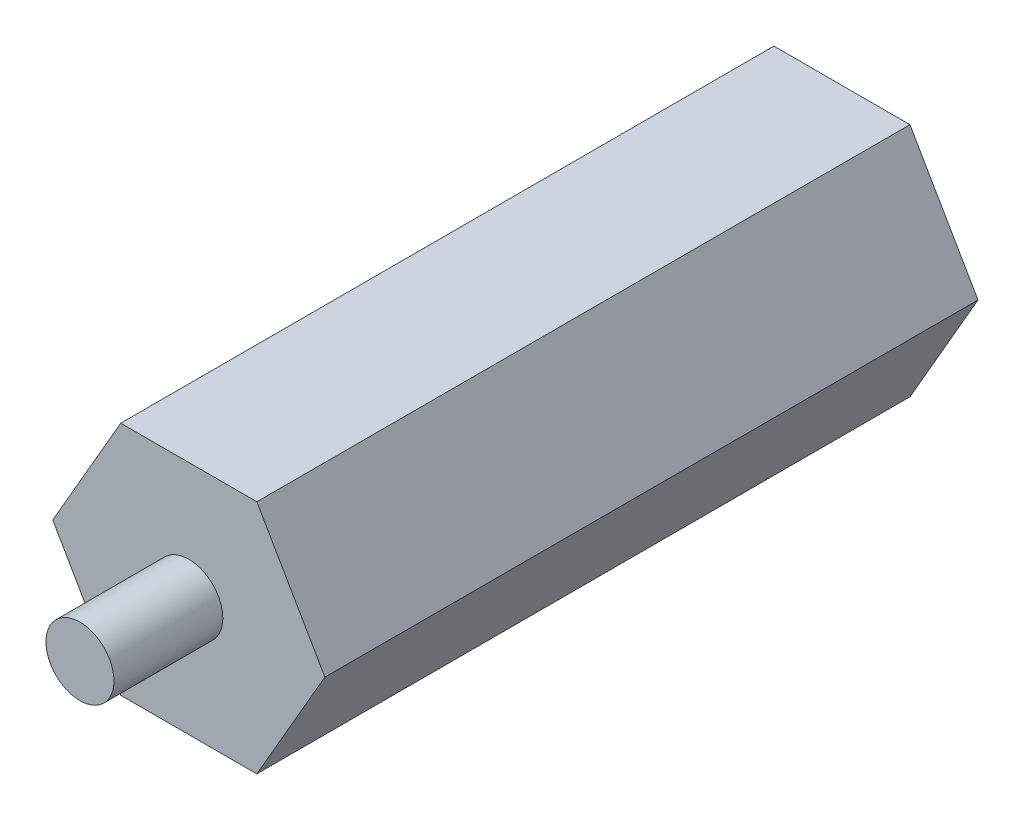
SolidWorks part; units mm, degrees
ref_plane "Alzado" through (0, 0, 0) normal (0, 0, 1) x (1, 0, 0)
ref_plane "Planta" through (0, 0, 0) normal (0, 1, 0) x (1, 0, 0)
ref_plane "Vista lateral" through (0, 0, 0) normal (1, 0, 0) x (0, 0, -1)
sketch "Croquis2" plane through (0, 0, 0) normal (0, 0, 1) x (1, 0, 0)
  line L1 (-63.5, 0) -> (-31.75, -54.9926)
  line L2 (-31.75, -54.9926) -> (31.75, -54.9926)
  line L3 (31.75, -54.9926) -> (63.5, 0)
  line L4 (63.5, 0) -> (31.75, 54.9926)
  line L5 (31.75, 54.9926) -> (-31.75, 54.9926)
  line L6 (-31.75, 54.9926) -> (-63.5, 0)
  circle A0 centre (0, 0) radius 54.9926 construction
  dimension "D1" = 63.5
extrude "Saliente-Extruir1" add sketch "Croquis2" against normal blind 304.8
sketch "Croquis4" plane through (0, 0, 0) normal (0, 0, 1) x (1, 0, 0)
  circle A0 centre (0, 0) radius 15.875
  dimension "D1" = 31.75
extrude "Saliente-Extruir2" add sketch "Croquis4" along normal blind 50.8
sketch "Croquis5" plane through (0, 0, -304.8) normal (0, 0, -1) x (-1, 0, 0)
  circle A0 centre (0, 0) radius 15.875
extrude "Saliente-Extruir3" add sketch "Croquis5" along normal blind 25.4
